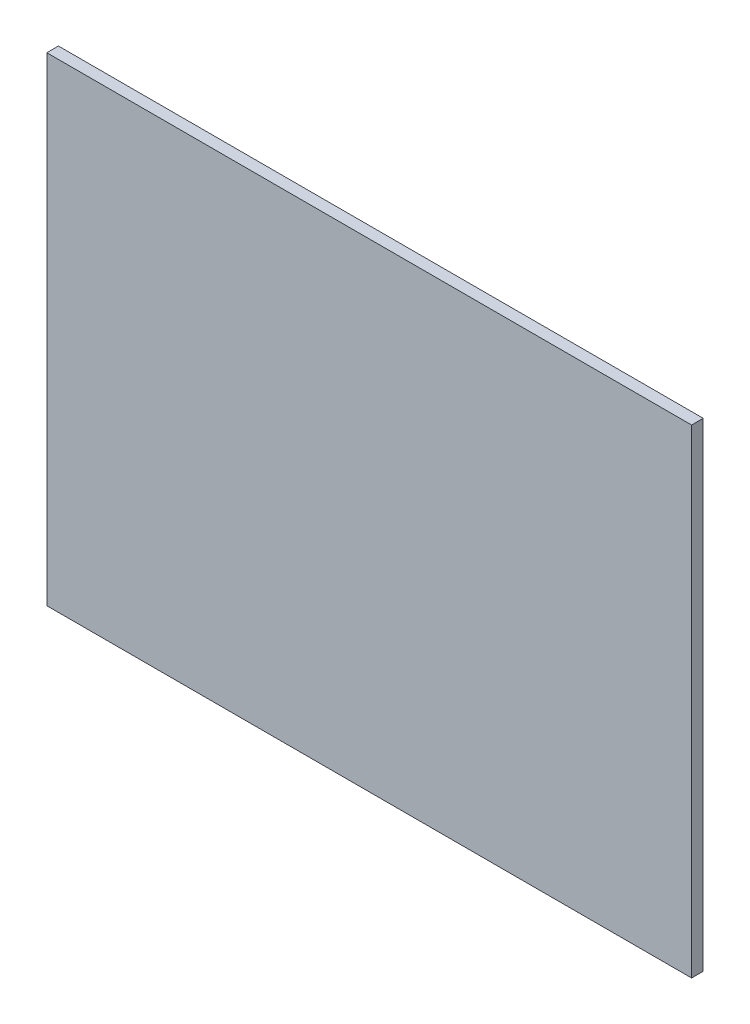
SolidWorks part; units mm, degrees
material "Pine"
ref_plane "Front Plane" through (0, 0, 0) normal (0, 0, 1) x (1, 0, 0)
ref_plane "Top Plane" through (0, 0, 0) normal (0, 1, 0) x (1, 0, 0)
ref_plane "Right Plane" through (0, 0, 0) normal (1, 0, 0) x (0, 0, -1)
sketch "Sketch1" plane through (0, 0, 0) normal (0, 0, 1) x (1, 0, 0)
  line L1 (-330.2409, 502.4442) -> (330.2409, 502.4442)
  line L2 (-330.2409, 502.4442) -> (-330.2409, 11.9062)
  line L3 (-330.2409, 11.9062) -> (330.2409, 11.9062)
  line L4 (330.2409, 502.4442) -> (330.2409, 11.9062)
extrude "Boss-Extrude1" add sketch "Sketch1" against normal up to surface (11.9063 mm away)
